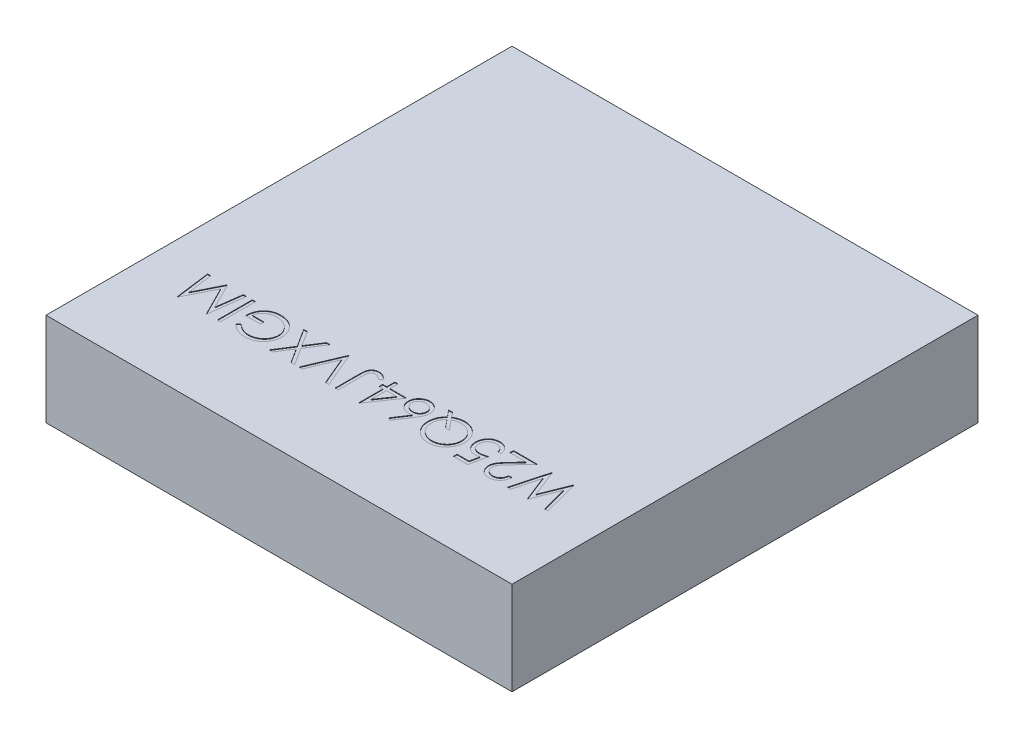
SolidWorks part; units mm, degrees
ref_plane "Front Plane" through (0, 0, 0) normal (0, 0, 1) x (1, 0, 0)
ref_plane "Top Plane" through (0, 0, 0) normal (0, 1, 0) x (1, 0, 0)
ref_plane "Right Plane" through (0, 0, 0) normal (1, 0, 0) x (0, 0, -1)
sketch "BaseS" plane through (0, 0, 0) normal (0, 1, 0) x (1, 0, 0)
  line L1 (-2, 2) -> (2, 2)
  line L2 (-2, 2) -> (-2, -2)
  line L3 (-2, -2) -> (2, -2)
  line L4 (2, 2) -> (2, -2)
  line L5 (-2, 2) -> (2, -2) construction
  line L6 (-2, -2) -> (2, 2) construction
  point P0 (0, 0)
  dimension "Dim" = 4
extrude "Base" add sketch "BaseS" along normal blind 0.8
sketch "PartNumberS" plane through (0, 0.8, 0) normal (0, 1, 0) x (1, 0, 0)
  line L0 (2, -1) -> (-2, -1) construction
  line L1 (2, -2) -> (2, 2) construction
  line L2 (-2, 2) -> (-2, -2) construction
  line L3 (-2, -2) -> (2, -2) construction
  text T0 "W25Q64JVXGIM" font "Century Gothic" height 0.3
  dimension "YDim" = 1
extrude "PartNumber" cut sketch "PartNumberS" against normal blind 0.005
